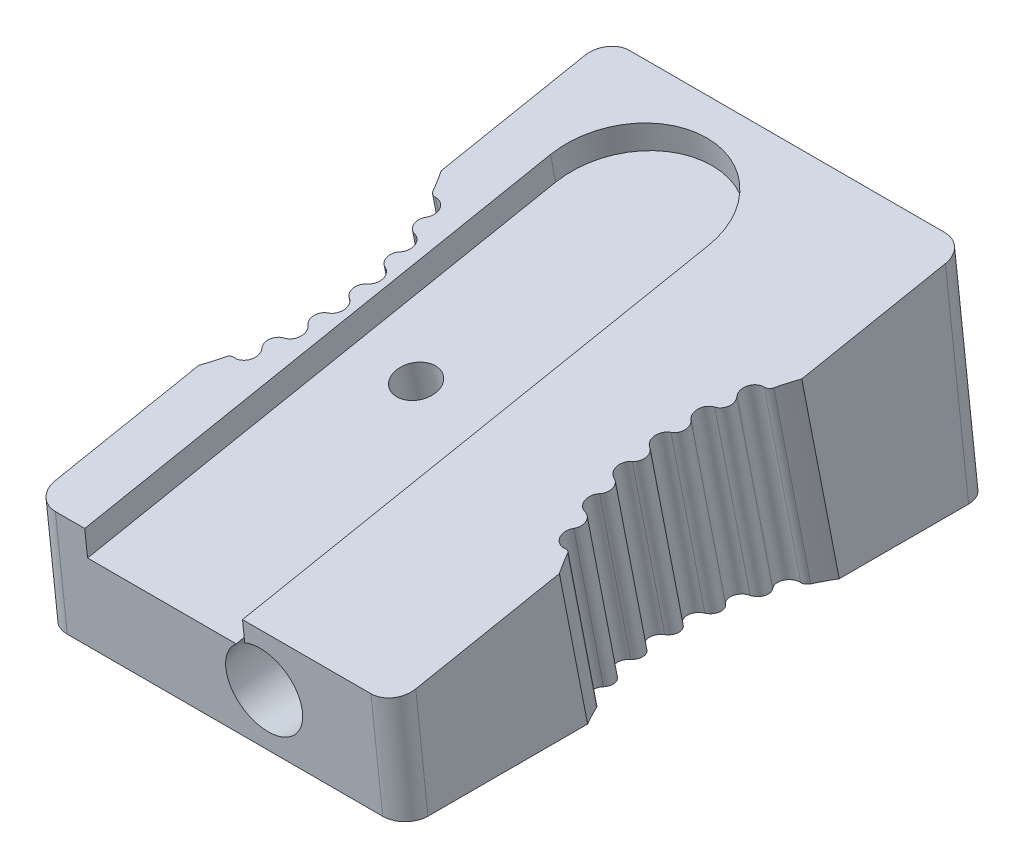
SolidWorks part; units mm, degrees
material "1060 Alloy"
ref_plane "Front Plane" through (0, 0, 0) normal (0, 0, 1) x (1, 0, 0)
ref_plane "Top Plane" through (0, 0, 0) normal (0, 1, 0) x (1, 0, 0)
ref_plane "Right Plane" through (0, 0, 0) normal (1, 0, 0) x (0, 0, -1)
sketch "Sketch1" plane through (0, 0, 0) normal (1, 0, 0) x (0, 0, -1)
  line L0 (13, 0) -> (-13, 0)
  line L1 (13, 0) -> (11.9542, 9.95)
  line L2 (11.9542, 9.95) -> (-13.5226, 4.9726)
  line L3 (-13.5226, 4.9726) -> (-13, 0)
  dimension "D1" = 26
  dimension "D2" = 9.95
  dimension "D3" = 84
  dimension "D4" = 5
extrude "Boss-Extrude1" add sketch "Sketch1" along normal mid plane 16
sketch "Sketch2" plane through (0, 7.3346, 1.4329) normal (0, 0.9814, 0.1917) x (1, 0, 0)
  line L0 (-5.7, -12.9953) -> (-5.7, 8.7403)
  line L2 (1.3, 8.7403) -> (1.3, -12.9953)
  line L4 (-8, 13.6403) -> (-8, -12.3183) construction
  line L5 (8, 13.6403) -> (-8, 13.6403) construction
  line L6 (-5.7, -12.9953) -> (1.3, -12.9953)
  arc A0 (-5.7, 8.7403) -> (1.3, 8.7403) centre (-2.2, 8.7403) cw
  point P2 (1.3, -12.9953)
  point P3 (1.3218, -13.001)
  dimension "D1" = 2.3
  dimension "D2" = 3.5
  dimension "D3" = 1.4
extrude "Cut-Extrude2" cut sketch "Sketch2" against normal blind 1.2
sketch "Sketch5" plane through (0, 7.3346, 1.4329) normal (0, 0.9814, 0.1917) x (1, 0, 0)
  line L0 (8, 13.6403) -> (8, -12.3183) construction
  line L1 (0, 13.6403) -> (0, -12.7588) construction
  line L2 (8, 13.6403) -> (-8, 13.6403) construction
  line L3 (8, -12.7588) -> (-8, -12.7588) construction
  line L4 (8, -12.3183) -> (1.3, -12.3183) construction
  line L5 (-8, 6.1403) -> (-8, -4.8183)
  line L6 (8, 6.1403) -> (8, -4.8183)
  arc A0 (8, 6.1403) -> (8, -4.8183) centre (17.2574, 0.661) ccw
  arc A1 (-8, 6.1403) -> (-8, -4.8183) centre (-17.2574, 0.661) cw
  point P17 (6.5, 0.661)
  dimension "D1" = 7.5
  dimension "D3" = 13
  dimension "D2" = 7.5
extrude "Cut-Extrude3" cut sketch "Sketch5" against normal through all
ref_plane "Plane1" through (2, 0, 0) normal (1, 0, 0) x (0, 0, -1)
fillet "Fillet1" radius 1 4 edges at (-8, 4.975, -12.4771) (8, 4.975, -12.4771) (-8, 2.4863, 13.2613) (8, 2.4863, 13.2613)
sketch "Sketch6" plane through (2, 0, 0) normal (1, 0, 0) x (0, 0, -1)
  line L0 (-13.2613, 2.4863) -> (12.4771, 4.975) construction
  line L1 (-13.5226, 4.9726) -> (-13, 0) construction
  line L2 (13, 0) -> (11.9542, 9.95) construction
  line L5 (-14.5172, 4.8681) -> (-13.9945, -0.1045)
  line L6 (-14.4251, 3.9923) -> (-14.2821, 2.6316)
  line L7 (-14.2567, 2.3901) -> (13.4725, 5.0712)
  line L8 (13.9945, 0.1045) -> (12.9487, 10.0545)
  line L9 (13.4725, 5.0712) -> (13.0451, 9.1378)
  line L10 (-14.4251, 3.9923) -> (13.0451, 9.1378)
  line L11 (-14.4251, 3.9923) -> (-14.2567, 2.3901)
  line L12 (13.0451, 9.1378) -> (13.4725, 5.0712)
  point P15 (-13.439, 4.177)
  point P16 (12.059, 8.9531)
  point P17 (-13.375, 3.5681)
  point P18 (12.1515, 8.0731)
  dimension "D1" = 1
  dimension "D3" = 1.7
  dimension "D4" = 4
  dimension "D2" = 1
revolve "Cut-Revolve1" cut sketch "Sketch6" angle 360 about L7
hole_wizard "M2.2x0.45 Tapped Hole1" positions "Sketch7" profile "Sketch8" tap size "M2.2x0.45" standard "ANSI Metric"
sketch "Sketch7" plane through (0, 6.1568, 1.2029) normal (0, 0.9814, 0.1917) x (1, 0, 0)
  line L0 (-2.9, -0.4244) -> (-2.9, -12.4244) construction
  line L1 (0.8986, -12.4244) -> (-5.7, -12.4244) construction
  line L4 (-2.9, -0.4244) -> (-5.7, -0.4244) construction
  line L5 (-5.7, 8.7403) -> (-5.7, -12.4244) construction
  point P3 (-2.9, -0.4244)
  dimension "D1" = 2.8
  dimension "D2" = 12
sketch "Sketch8" plane through (-2.9, 6.0755, 1.6194) normal (1, 0, 0) x (0, -0.1917, 0.9814)
  line L0 (0, 0) -> (0, 4)
  line L1 (0, 4) -> (0.875, 3.4742)
  line L2 (0.875, 3.4742) -> (0.875, 0)
  line L5 (0.875, 0) -> (0, 0)
  line L10 (0, 4) -> (-0.875, 3.4742) construction
  line L11 (0, -6.35) -> (0, 107.95) construction
  dimension "Tap Drill Dia." = 1.75
  dimension "Tap Drill Depth" = 4
  dimension "Drill Angle" = 118
cosmetic thread "Hole Thread1" parameters "D1"=4, "D2"=2.2
sketch "Sketch9" plane through (0, 7.3346, 1.4329) normal (0, 0.9814, 0.1917) x (1, 0, 0)
  line L0 (0, 13.6403) -> (0, -12.4244) construction
  line L1 (7, 13.6403) -> (-7, 13.6403) construction
  line L2 (0.8986, -12.4244) -> (-5.7, -12.4244) construction
  arc A0 (7.2898, 5.1597) -> (6.8979, 4.3272) centre (7.2709, 4.6601) ccw
  arc A1 (8, 6.1403) -> (8, -4.8183) centre (17.2574, 0.661) ccw construction
  arc A2 (6.6609, 3.5721) -> (6.459, 2.6998) centre (6.7768, 3.0858) ccw
  arc A3 (6.3403, 1.9174) -> (6.2743, 1.0244) centre (6.5293, 1.4545) ccw
  arc A4 (6.2766, 0.233) -> (6.3479, -0.6596) centre (6.5342, -0.1955) ccw
  arc A5 (6.4712, -1.4413) -> (6.6782, -2.3124) centre (6.7913, -1.8254) ccw
  arc A6 (6.9196, -3.0661) -> (7.3598, -3.8925) centre (7.2946, -3.3967) ccw
  arc A7 (6.8979, 4.3272) -> (6.6609, 3.5721) centre (6.554, 4.0204) cw
  arc A8 (6.459, 2.6998) -> (6.3403, 1.9174) centre (6.1661, 2.344) cw
  arc A9 (6.2743, 1.0244) -> (6.2766, 0.233) centre (6.0392, 0.628) cw
  arc A10 (6.3479, -0.6596) -> (6.4712, -1.4413) centre (6.1762, -1.0872) cw
  arc A11 (6.6782, -2.3124) -> (6.9196, -3.0661) centre (6.5739, -2.7613) cw
  arc A12 (7.3598, -3.8925) -> (7.5635, -4.0026) centre (7.3855, -4.0882) cw
  arc A13 (7.2898, 5.1597) -> (7.5635, 5.3246) centre (7.3008, 5.451) ccw
  arc A14 (7.5635, 5.3246) -> (7.5635, -4.0026) centre (17.2574, 0.661) ccw
  arc A15 (-7.5635, 5.3246) -> (-7.5635, -4.0026) centre (-17.2574, 0.661) cw
  arc A16 (-7.2898, 5.1597) -> (-7.5635, 5.3246) centre (-7.3008, 5.451) cw
  arc A17 (-7.3598, -3.8925) -> (-7.5635, -4.0026) centre (-7.3855, -4.0882) ccw
  arc A18 (-6.6782, -2.3124) -> (-6.9196, -3.0661) centre (-6.5739, -2.7613) ccw
  arc A19 (-6.3479, -0.6596) -> (-6.4712, -1.4413) centre (-6.1762, -1.0872) ccw
  arc A20 (-6.2743, 1.0244) -> (-6.2766, 0.233) centre (-6.0392, 0.628) ccw
  arc A21 (-6.459, 2.6998) -> (-6.3403, 1.9174) centre (-6.1661, 2.344) ccw
  arc A22 (-6.8979, 4.3272) -> (-6.6609, 3.5721) centre (-6.554, 4.0204) ccw
  arc A23 (-6.9196, -3.0661) -> (-7.3598, -3.8925) centre (-7.2946, -3.3967) cw
  arc A24 (-6.4712, -1.4413) -> (-6.6782, -2.3124) centre (-6.7913, -1.8254) cw
  arc A25 (-6.2766, 0.233) -> (-6.3479, -0.6596) centre (-6.5342, -0.1955) cw
  arc A26 (-6.3403, 1.9174) -> (-6.2743, 1.0244) centre (-6.5293, 1.4545) cw
  arc A27 (-6.6609, 3.5721) -> (-6.459, 2.6998) centre (-6.7768, 3.0858) cw
  arc A28 (-7.2898, 5.1597) -> (-6.8979, 4.3272) centre (-7.2709, 4.6601) cw
  point P31 (6.8533, -3.6318)
  arc M4 (-8, 6.1403) -> (-8, -4.8183) centre (-17.2574, 0.661) cw
  arc M14 (8, -4.8183) -> (8, 6.1403) centre (17.2574, 0.661) cw
  dimension "D1" = 1
  dimension "D8" = 1.65
  dimension "D2" = 1.65
  dimension "D3" = 1.65
  dimension "D4" = 1.65
  dimension "D5" = 1.65
  dimension "D6" = 1.65
  dimension "D7" = 1.65
extrude "Cut-Extrude4" cut sketch "Sketch9" against normal through all contours A28 A16 A22 M4 | A27 A22 A15 A21 | A26 A21 A15 A20 | A25 A20 A15 A19 | A24 A19 A15 A18 | A23 A18 A15 A17 | A6 A12 A11 M14 | A5 A11 A10 M14 | A4 A10 A9 M14 | A3 A9 A8 M14 | A2 A8 A7 M14 | A13 A0 A7 M14
